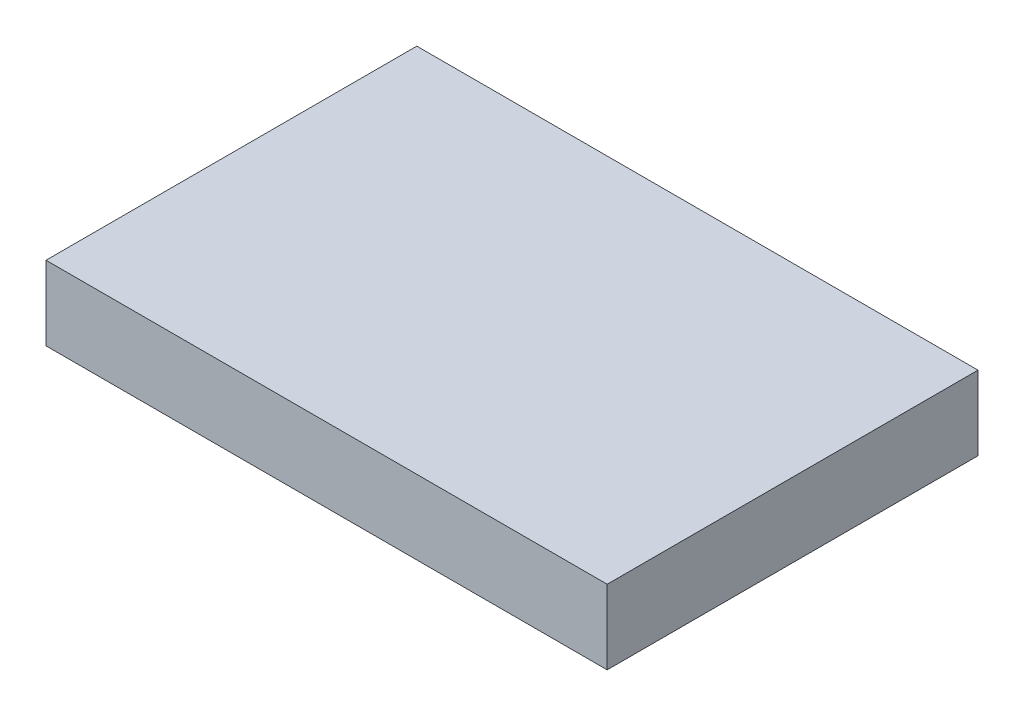
SolidWorks part; units mm, degrees
ref_plane "Front" through (0, 0, 0) normal (0, 0, 1) x (1, 0, 0)
ref_plane "Top" through (0, 0, 0) normal (0, 1, 0) x (1, 0, 0)
ref_plane "Right" through (0, 0, 0) normal (1, 0, 0) x (0, 0, -1)
sketch "Sketch1" plane through (0, 0, 0) normal (0, 1, 0) x (1, 0, 0)
  line L1 (0, 0) -> (22.7, 0)
  line L2 (0, 0) -> (0, -15)
  line L3 (0, -15) -> (22.7, -15)
  line L4 (22.7, 0) -> (22.7, -15)
  dimension "D1" = 15
  dimension "D2" = 22.7
extrude "Boss-Extrude1" add sketch "Sketch1" along normal blind 3
